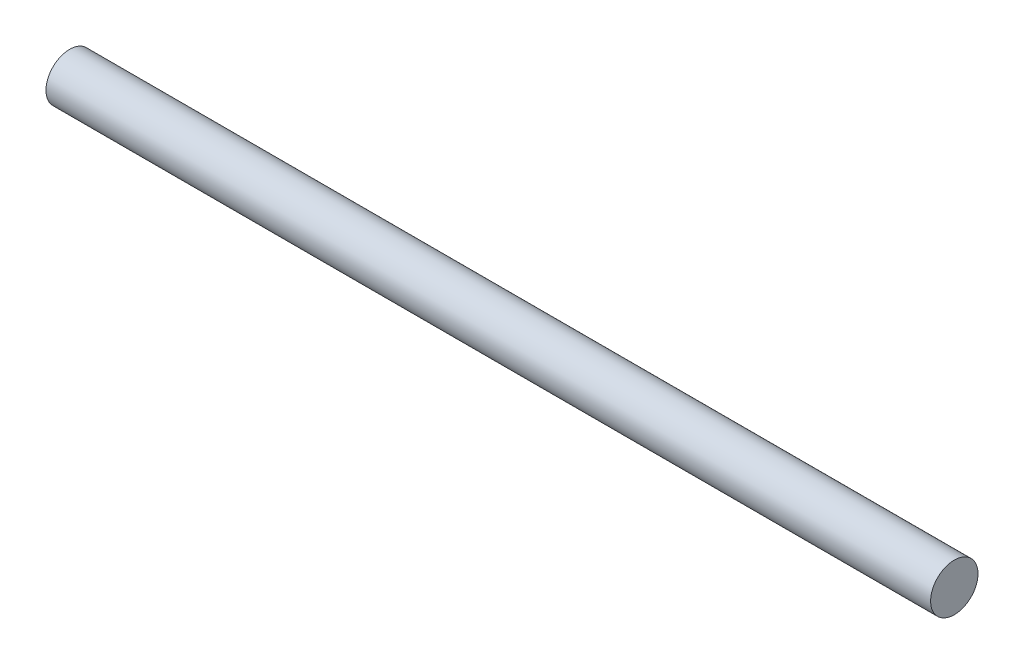
SolidWorks part; units mm, degrees
ref_plane "Front Plane" through (0, 0, 0) normal (0, 0, 1) x (1, 0, 0)
ref_plane "Top Plane" through (0, 0, 0) normal (0, 1, 0) x (1, 0, 0)
ref_plane "Right Plane" through (0, 0, 0) normal (1, 0, 0) x (0, 0, -1)
sketch "Sketch2" plane through (0, 0, 0) normal (1, 0, 0) x (0, 0, -1)
  circle A0 centre (0, 0) radius 15
  dimension "D1" = 30
extrude "Boss-Extrude1" add sketch "Sketch2" along normal blind 560
